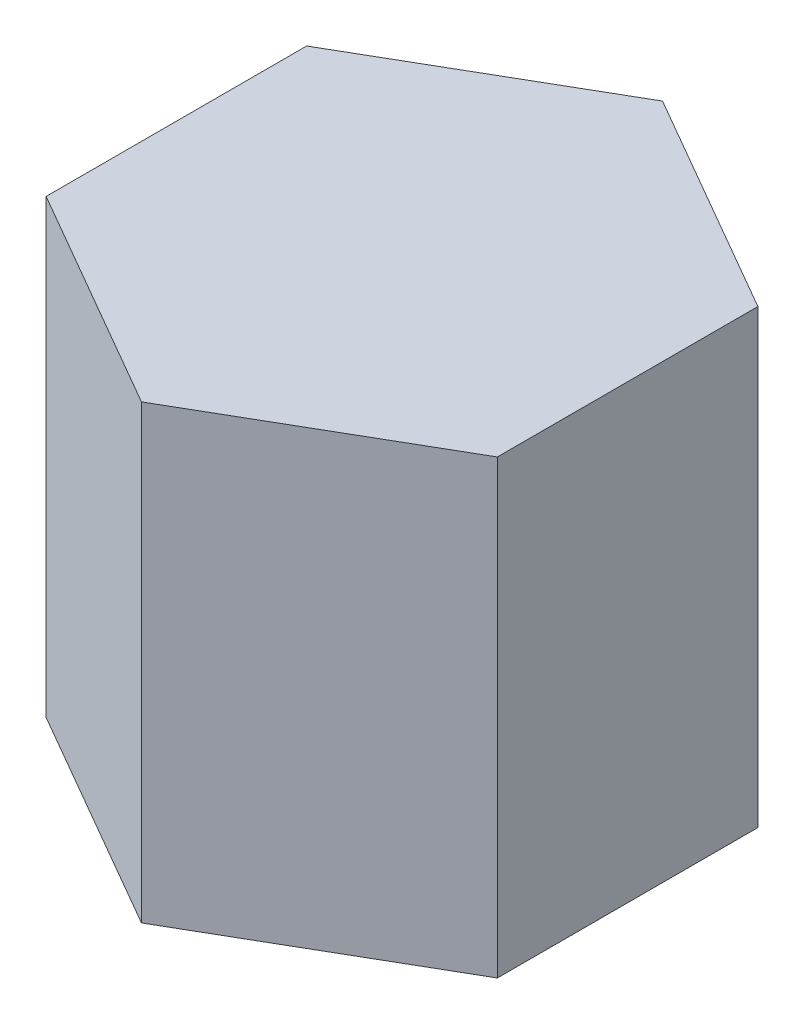
SolidWorks part; units mm, degrees
ref_plane "Front Plane" through (0, 0, 0) normal (0, 0, 1) x (1, 0, 0)
ref_plane "Top Plane" through (0, 0, 0) normal (0, 1, 0) x (1, 0, 0)
ref_plane "Right Plane" through (0, 0, 0) normal (1, 0, 0) x (0, 0, -1)
sketch "Sketch1" plane through (0, 0, 0) normal (0, 1, 0) x (1, 0, 0)
  line L1 (50, -28.8675) -> (50, 28.8675)
  line L2 (50, 28.8675) -> (0, 57.735)
  line L3 (0, 57.735) -> (-50, 28.8675)
  line L4 (-50, 28.8675) -> (-50, -28.8675)
  line L5 (-50, -28.8675) -> (0, -57.735)
  line L6 (0, -57.735) -> (50, -28.8675)
  line L12 (50, 28.8675) -> (50, -28.8675)
  line L16 (50, -28.8675) -> (0, -57.735)
  circle A0 centre (0, 0) radius 50 construction
  point P10 (56.7272, 0)
  point P16 (30.3015, -47.5163)
  dimension "D1" = 100
extrude "Boss-Extrude1" add sketch "Sketch1" along normal blind 100 contours L5 L6 L1 L2 L3 L4
